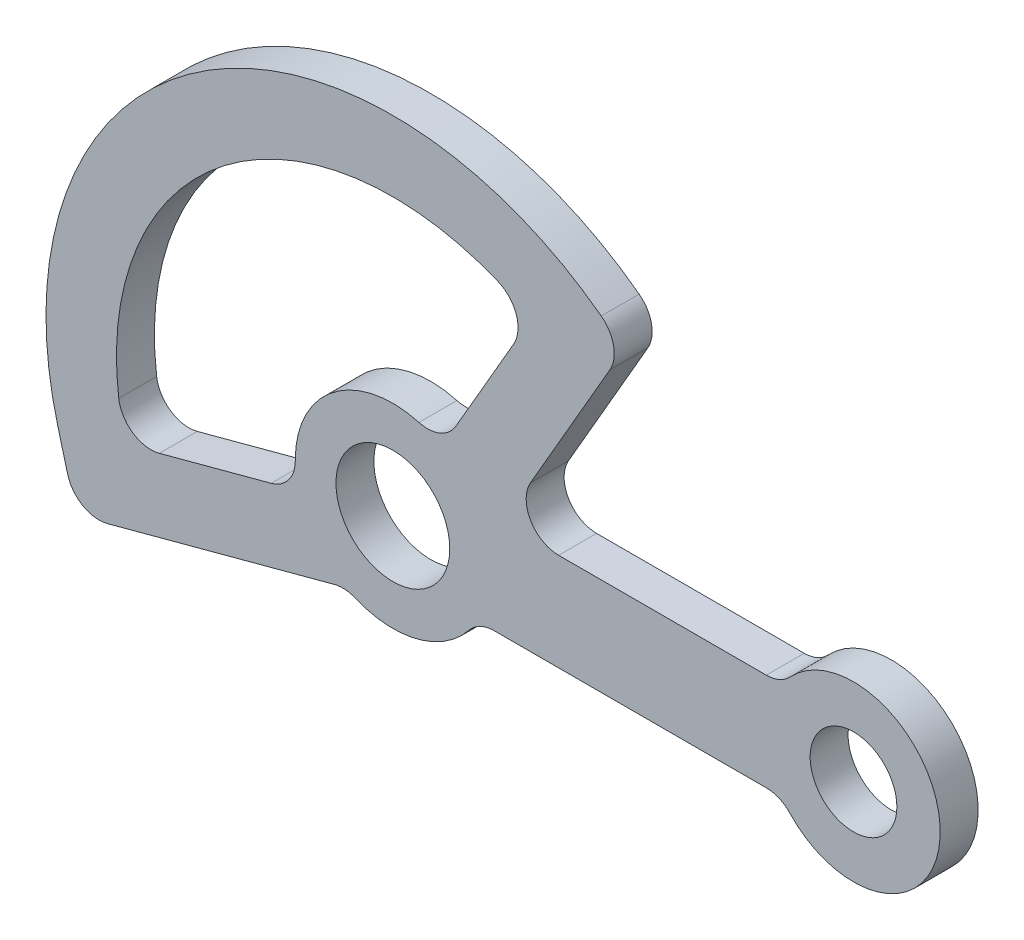
SolidWorks part; units mm, degrees
ref_plane "Front Plane" through (0, 0, 0) normal (0, 0, 1) x (1, 0, 0)
ref_plane "Top Plane" through (0, 0, 0) normal (0, 1, 0) x (1, 0, 0)
ref_plane "Right Plane" through (0, 0, 0) normal (1, 0, 0) x (0, 0, -1)
sketch "Sketch1" plane through (0, 0, 0) normal (0, 0, 1) x (1, 0, 0)
  line L0 (0, -10.5) -> (0, -18) construction
  line L1 (0, -131.2718) -> (0, -51) construction
  line L3 (25.4034, 18) -> (40.0463, 43.3623)
  line L4 (-22.4461, -6.0144) -> (-43.0786, -11.5429)
  line L5 (93, 0) -> (218.0399, 0) construction
  line L6 (218.0399, 0) -> (93, 0) construction
  line L7 (0, -51) -> (0, -131.2718) construction
  line L8 (0, -18) -> (0, -10.5) construction
  line L9 (-10.7986, -16.3521) -> (-52.6591, -27.5685)
  line L10 (22.2991, 38.6232) -> (11.619, 20.1246)
  line L12 (68.9065, 9) -> (30.5996, 9)
  line L13 (68.9065, -9) -> (18.735, -9)
  line L14 (0, 10.5) -> (0, 126.0729) construction
  line L16 (-61.8193, -16.5644) -> (-60.0075, -23.3259)
  circle A0 centre (0, 0) radius 10.5
  arc A1 (4.8171, 17.3435) -> (-17.9993, -0.1641) centre (0, 0) ccw
  circle A2 centre (85, 0) radius 8
  arc A3 (73.2957, -10.9091) -> (73.2957, 10.9091) centre (85, 0) ccw
  arc A6 (-6.9343, -16.6107) -> (14.0512, -11.25) centre (0, 0) ccw
  arc A7 (19.3833, 47.1729) -> (-50.5823, -6.5136) centre (0, 0) ccw
  arc A8 (38.4554, 51.1584) -> (-61.8193, -16.5644) centre (0, 0) ccw
  arc A9 (68.9065, 9) -> (73.2957, 10.9091) centre (68.9065, 15) ccw
  arc A10 (68.9065, -9) -> (73.2957, -10.9091) centre (68.9065, -15) cw
  arc A11 (18.735, -9) -> (14.0512, -11.25) centre (18.735, -15) ccw
  arc A12 (-10.7986, -16.3521) -> (-6.9343, -16.6107) centre (-9.2457, -22.1476) cw
  arc A13 (30.5996, 9) -> (25.4034, 18) centre (30.5996, 15) cw
  arc A14 (4.8171, 17.3435) -> (11.619, 20.1246) centre (6.4228, 23.1246) ccw
  arc A15 (38.4554, 51.1584) -> (40.0463, 43.3623) centre (34.8502, 46.3623) cw
  arc A16 (19.3833, 47.1729) -> (22.2991, 38.6232) centre (17.103, 41.6232) cw
  arc A17 (-50.5823, -6.5136) -> (-43.0786, -11.5429) centre (-44.6315, -5.7473) ccw
  arc A18 (-22.4461, -6.0144) -> (-17.9993, -0.1641) centre (-23.999, -0.2189) ccw
  arc A19 (-60.0075, -23.3259) -> (-52.6591, -27.5685) centre (-54.212, -21.773) ccw
  point P31 (-8.661, -15.7793)
  point P38 (9, 15.5885)
  point P43 (25.5, 44.1673)
  point P46 (-49.2622, -13.1998)
  point P49 (-17.3867, -4.6587)
  point P52 (-58.4546, -29.1215)
  dimension "D1" = 21
  dimension "D2" = 36
  dimension "D3" = 16
  dimension "D4" = 32
  dimension "D6" = 13
  dimension "D7" = 64
  dimension "D8" = 51
  dimension "D17" = 6
  dimension "D5" = 85
  dimension "D9" = 13
  dimension "D10" = 15
  dimension "D11" = 30
  dimension "D12" = 9
  dimension "D13" = 9
  dimension "D14" = 33
  dimension "D15" = 33
  dimension "D16" = 13
extrude "Boss-Extrude1" add sketch "Sketch1" along normal blind 7
